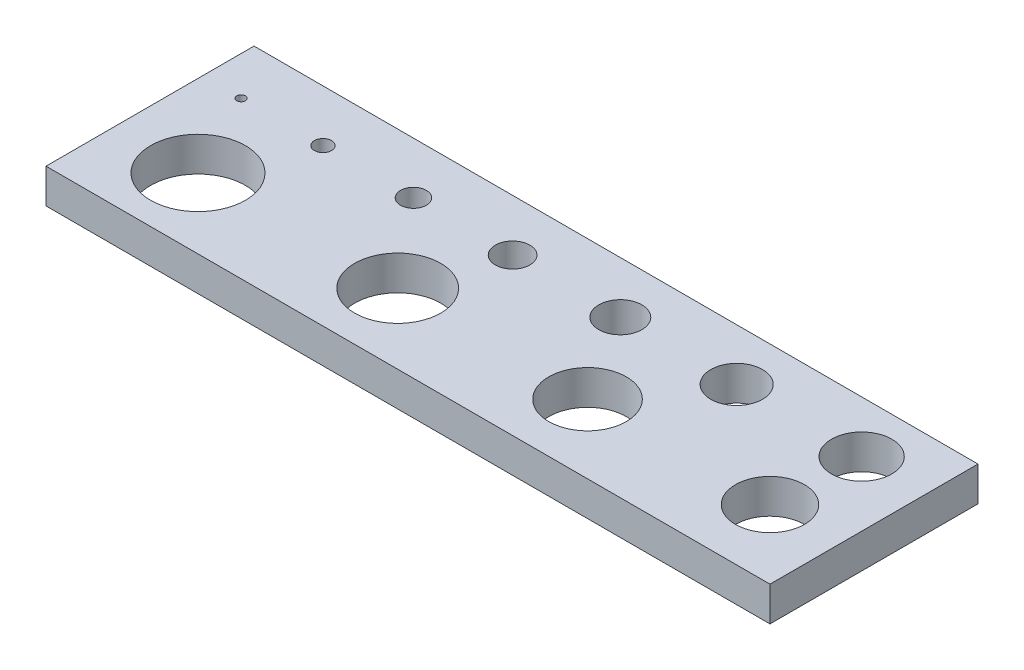
SolidWorks part; units mm, degrees
ref_plane "Front Plane" through (0, 0, 0) normal (0, 0, 1) x (1, 0, 0)
ref_plane "Top Plane" through (0, 0, 0) normal (0, 1, 0) x (1, 0, 0)
ref_plane "Right Plane" through (0, 0, 0) normal (1, 0, 0) x (0, 0, -1)
sketch "Sketch1" plane through (0, 0, 0) normal (0, 1, 0) x (1, 0, 0)
  line L0 (1.25, 0) -> (21.25, 0) construction
  line L1 (26.25, 0) -> (46.25, 0) construction
  line L2 (53.75, 0) -> (73.75, 0) construction
  line L3 (83.75, 0) -> (103.75, 0) construction
  line L4 (116.25, 0) -> (136.25, 0) construction
  line L5 (151.25, 0) -> (171.25, 0) construction
  line L6 (26.25, -25) -> (57.9182, -25) construction
  line L7 (168.75, -25.3422) -> (137.0818, -25.3422) construction
  line L8 (114.5818, -25.3422) -> (82.9135, -25.3422) construction
  line L10 (-1.25, 0) -> (-1.25, -25) construction
  line L11 (-11.25, -45.3422) -> (198.75, -45.3422)
  line L12 (-11.25, -45.3422) -> (-11.25, 15)
  line L13 (188.75, -25.3422) -> (188.75, 0) construction
  line L14 (-11.25, 15) -> (198.75, 15)
  line L15 (198.75, -45.3422) -> (198.75, 15)
  line L16 (-11.25, -45.3422) -> (198.75, 15) construction
  line L17 (-11.25, 15) -> (198.75, -45.3422) construction
  circle A0 centre (0, 0) radius 1.25
  circle A1 centre (23.75, 0) radius 2.5
  circle A2 centre (50, 0) radius 3.75
  circle A3 centre (78.75, 0) radius 5
  circle A4 centre (110, 0) radius 6.25
  circle A5 centre (143.75, 0) radius 7.5
  circle A6 centre (180, 0) radius 8.75
  circle A7 centre (178.75, -25.3422) radius 10
  circle A8 centre (125.8318, -25.3422) radius 11.25
  circle A9 centre (70.4182, -25) radius 12.5
  circle A10 centre (12.5, -25) radius 13.75
  point P51 (93.75, -15.1711)
  dimension "D1" = 2.5
  dimension "D2" = 5
  dimension "D3" = 7.5
  dimension "D4" = 10
  dimension "D5" = 12.5
  dimension "D6" = 15
  dimension "D7" = 17.5
  dimension "D8" = 20
  dimension "D9" = 22.5
  dimension "D10" = 25
  dimension "D11" = 27.5
  dimension "D12" = 25
  dimension "D13" = 20
  dimension "D14" = 10
  dimension "D15" = 10
  dimension "D16" = 15
  dimension "D17" = 20
extrude "Boss-Extrude1" add sketch "Sketch1" along normal blind 10
